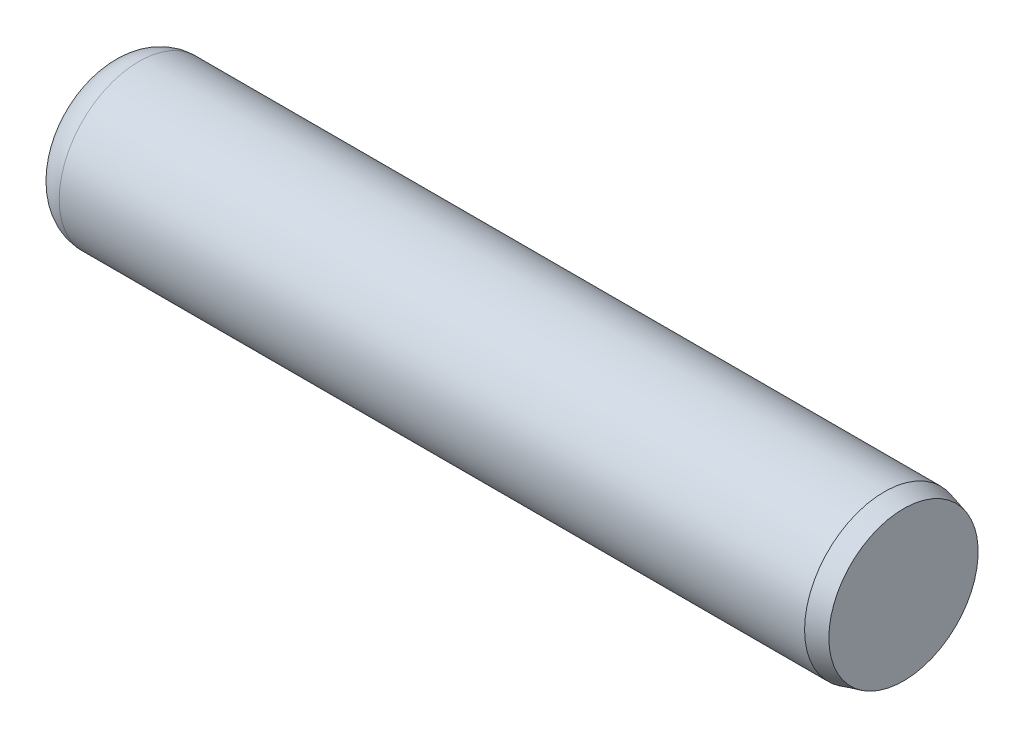
SolidWorks part; units mm, degrees
ref_plane "Plane1" through (0, 0, 0) normal (0, 0, 1) x (1, 0, 0)
ref_plane "Plane2" through (0, 0, 0) normal (0, 1, 0) x (1, 0, 0)
ref_plane "Plane3" through (0, 0, 0) normal (1, 0, 0) x (0, 0, -1)
sketch "Sketch1" plane through (0, 0, 0) normal (0, 0, 1) x (1, 0, 0)
  line L1 (-6.35, 0) -> (107.95, 0) construction
  line L2 (0, 0) -> (15.875, 0)
  line L3 (15.875, 0) -> (15.875, 1.4878)
  line L4 (15.875, 1.4878) -> (15.4934, 1.59)
  line L5 (15.4934, 1.59) -> (0.636, 1.59)
  line L6 (0, 0.954) -> (0, 0)
  arc A0 (0.636, 1.59) -> (0, 0.954) centre (0.636, 0.954) ccw
  dimension "D4" = 0.636
  dimension "D2" = 0.3816
  dimension "D3" = 15
  dimension "Diameter" = 3.1801
  dimension "Length" = 15.875
revolve "Base-Revolve" add sketch "Sketch1" angle 360 about L1
equation "\"D4@Sketch1\" = \"Diameter@Sketch1\" * 0.2"
equation "\"D2@Sketch1\" = \"Diameter@Sketch1\" * 0.12"
equation "\"D3@Sketch1\" = 15.0"
